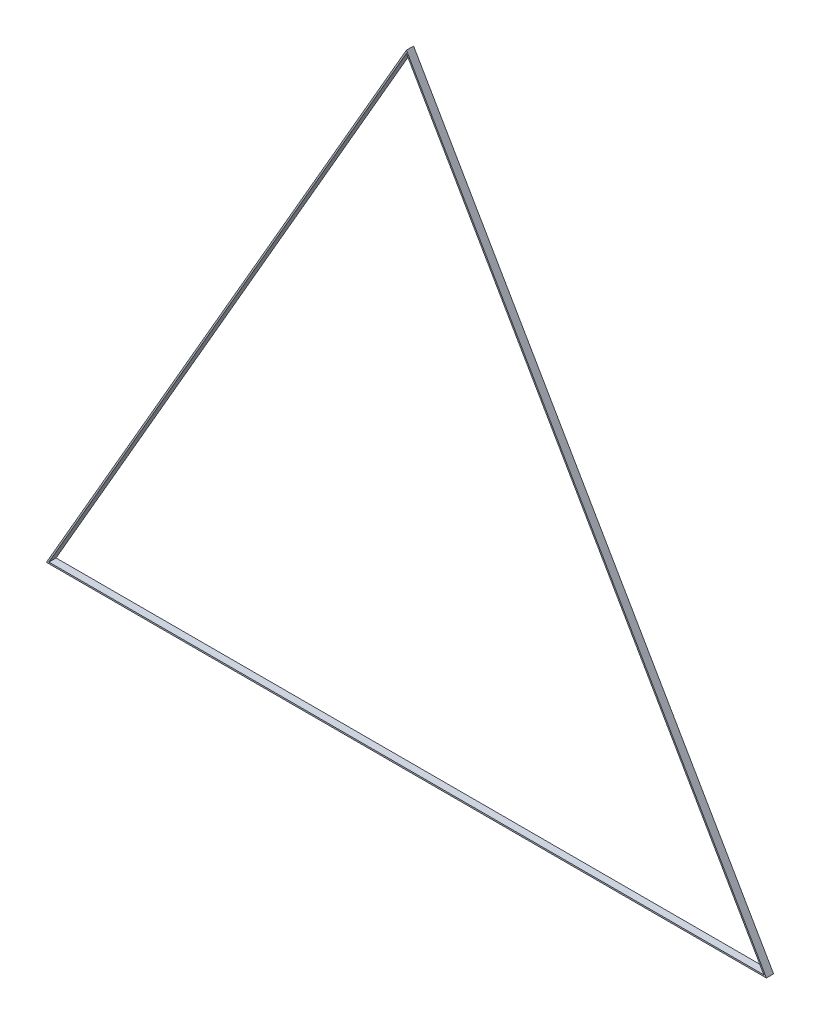
SolidWorks part; units mm, degrees
ref_plane "Plan de face" through (0, 0, 0) normal (0, 0, 1) x (1, 0, 0)
ref_plane "Plan de dessus" through (0, 0, 0) normal (0, 1, 0) x (1, 0, 0)
ref_plane "Plan de droite" through (0, 0, 0) normal (1, 0, 0) x (0, 0, -1)
sketch "Esquisse1" plane through (0, 0, 0) normal (0, 0, 1) x (1, 0, 0)
  line L0 (-500, 0) -> (0, 866.0254)
  line L1 (0, 866.0254) -> (500, 0)
  line L2 (500, 0) -> (-500, 0)
  point P2 (0, 0)
  dimension "D1" = 60
  dimension "D2" = 60
  dimension "D3" = 1000
extrude "Boss.-Extru.1" add sketch "Esquisse1" along normal blind 10
sketch "Esquisse2" plane through (0, 0, 10) normal (0, 0, 1) x (1, 0, 0)
  line L0 (-496.5359, 2) -> (0, 862.0254)
  line L1 (0, 862.0254) -> (496.5359, 2)
  line L2 (496.5359, 2) -> (-496.5359, 2)
  line L3 (-500, 0) -> (500, 0) construction
  line L4 (0, 866.0254) -> (-500, 0) construction
  line L5 (500, 0) -> (0, 866.0254) construction
  dimension "D1" = 2
  dimension "D2" = 2
  dimension "D3" = 2
extrude "Enlèv. mat.-Extru.1" cut sketch "Esquisse2" against normal blind 10
